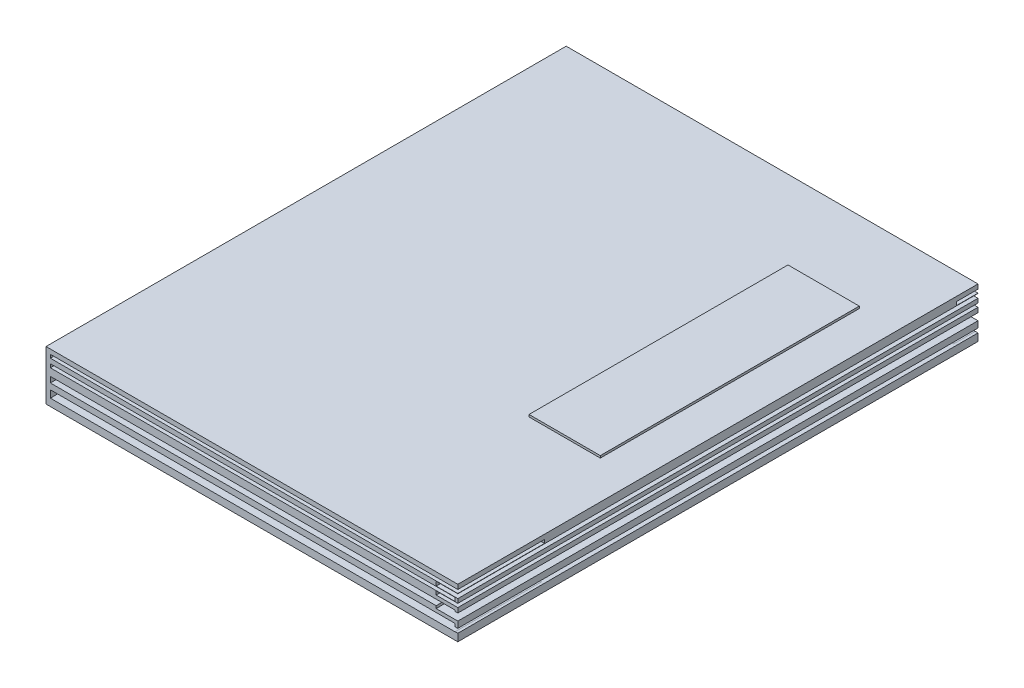
SolidWorks part; units mm, degrees
ref_plane "前视基准面" through (0, 0, 0) normal (0, 0, 1) x (1, 0, 0)
ref_plane "上视基准面" through (0, 0, 0) normal (0, 1, 0) x (1, 0, 0)
ref_plane "右视基准面" through (0, 0, 0) normal (1, 0, 0) x (0, 0, -1)
sketch "草图1" plane through (0, 0, 0) normal (0, 1, 0) x (1, 0, 0)
  line L1 (-95, 125) -> (95, 125)
  line L2 (-95, 125) -> (-95, -115)
  line L3 (-95, -115) -> (95, -115)
  line L4 (95, 125) -> (95, -115)
  point P0 (0, 0)
extrude "凸台-拉伸1" add sketch "草图1" along normal blind 23
sketch "草图2" plane through (95, 0, 0) normal (1, 0, 0) x (0, 0, -1)
  line L1 (128.5392, 19.1887) -> (-116.4147, 19.1887)
  line L2 (128.5392, 19.1887) -> (128.5392, 17.2678)
  line L3 (128.5392, 17.2678) -> (-116.4147, 17.2678)
  line L4 (-116.4147, 19.1887) -> (-116.4147, 17.2678)
  line L5 (129.0094, 15.3627) -> (-116.7119, 15.3627)
  line L6 (129.0094, 15.3627) -> (129.0094, 13.679)
  line L7 (129.0094, 13.679) -> (-116.7119, 13.679)
  line L8 (-116.7119, 15.3627) -> (-116.7119, 13.679)
  line L9 (127.8189, 8.2957) -> (-116.7119, 8.2957)
  line L10 (127.8189, 8.2957) -> (127.8189, 11.5)
  line L11 (127.8189, 11.5) -> (-116.7119, 11.5)
  line L12 (-116.7119, 8.2957) -> (-116.7119, 11.5)
  line L13 (127.0838, 5.3696) -> (-116.4565, 5.3696)
  line L14 (127.0838, 5.3696) -> (127.0838, 3.4251)
  line L15 (127.0838, 3.4251) -> (-116.4565, 3.4251)
  line L16 (-116.4565, 5.3696) -> (-116.4565, 3.4251)
extrude "切除-拉伸1" cut sketch "草图2" against normal blind 10
sketch "草图3" plane through (0, 0, 115) normal (0, 0, 1) x (1, 0, 0)
  line L0 (95, 23) -> (95, 19.1887) construction
  line L1 (95, 19.3299) -> (-92.994, 19.3299)
  line L2 (95, 19.3299) -> (95, 20.9016)
  line L3 (95, 20.9016) -> (-92.994, 20.9016)
  line L4 (-92.994, 19.3299) -> (-92.994, 20.9016)
  line L6 (93.7585, 17.1483) -> (-92.994, 17.1483)
  line L7 (93.7585, 17.1483) -> (93.7585, 15.4844)
  line L8 (93.7585, 15.4844) -> (-92.994, 15.4844)
  line L9 (-92.994, 17.1483) -> (-92.994, 15.4844)
  line L10 (93.7585, 12.0577) -> (-92.994, 12.0577)
  line L11 (93.7585, 12.0577) -> (93.7585, 9.4388)
  line L12 (93.7585, 9.4388) -> (-92.994, 9.4388)
  line L13 (-92.994, 12.0577) -> (-92.994, 9.4388)
  line L14 (93.7585, 6.7145) -> (-92.994, 6.7145)
  line L15 (93.7585, 6.7145) -> (93.7585, 3.3684)
  line L16 (93.7585, 3.3684) -> (-92.994, 3.3684)
  line L17 (-92.994, 6.7145) -> (-92.994, 3.3684)
extrude "切除-拉伸2" cut sketch "草图3" against normal blind 40
sketch "草图4" plane through (0, 23, 0) normal (0, 1, 0) x (1, 0, 0)
  line L0 (-156.583, 0) -> (142.6497, 0) construction
ref_plane "基准面1" through (0, 0, 0) normal (0, 0, 1) x (1, 0, 0)
ref_plane "基准面2" through (0, 0, -20) normal (0, 0, 1) x (1, 0, 0)
mirror "镜向3" about plane through (0, 0, -20) normal (0, 0, 1) of "切除-拉伸2"
ref_plane "基准面3" through (0, 23, 0) normal (0, 1, 0) x (1, 0, 0)
sketch "草图7" plane through (0, 23, 0) normal (0, 1, 0) x (1, 0, 0)
  line L0 (-80.2819, 125) -> (-80.2819, -115)
  line L1 (95, 125) -> (-95, 125) construction
  line L2 (-95, -115) -> (95, -115) construction
  line L3 (-80.2819, -115) -> (-77.7275, -115)
  line L4 (-77.7275, -115) -> (-77.7275, 125)
  line L5 (-77.7275, 125) -> (-80.2819, 125)
  line L6 (-95, 102.2628) -> (-80.2819, 102.2628)
  line L7 (-95, 125) -> (-95, -115) construction
  line L8 (-95, 62.5024) -> (-80.2819, 62.5024)
  line L9 (-95, 20.5533) -> (-80.2819, 20.5533)
  line L10 (-95, -11.1821) -> (-80.2819, -11.1821)
  line L11 (-95, -49.8483) -> (-80.2819, -49.8483)
  line L12 (-95, -85.5962) -> (-80.2819, -85.5962)
ref_plane "基准面4" through (-95, 0, 0) normal (-1, 0, 0) x (0, 0, 1)
sketch "草图8" plane through (-95, 0, 0) normal (-1, 0, 0) x (0, 0, 1)
  line L0 (-102.2628, 23) -> (-102.2628, 0)
  line L1 (-125, 0) -> (115, 0) construction
  line L2 (-62.5024, 23) -> (-62.5024, 0)
  line L3 (-20.5533, 23) -> (-20.5533, 0)
  line L4 (11.1821, 23) -> (11.1821, 0)
  line L5 (49.8483, 23) -> (49.8483, 0)
  line L6 (85.5962, 23) -> (85.5962, 0)
sketch "草图9" plane through (0, 0, 0) normal (0, -1, 0) x (1, 0, 0)
  line L0 (-77.7275, 115) -> (-77.7275, -125)
  line L1 (-95, 85.5962) -> (-77.7275, 85.5962)
  line L2 (-95, 49.8483) -> (-77.7275, 49.8483)
  line L3 (-95, 11.1821) -> (-77.7275, 11.1821)
  line L4 (-95, -20.5533) -> (-77.7275, -20.5533)
  line L5 (-95, -62.5024) -> (-77.7275, -62.5024)
  line L6 (-94.9153, -101.4933) -> (-77.7275, -101.4933)
sketch "草图10" plane through (0, 23, 0) normal (0, 1, 0) x (1, 0, 0)
  line L1 (44.5752, 87.7564) -> (77.4585, 87.7564)
  line L2 (44.5752, 87.7564) -> (44.5752, -31.7197)
  line L3 (44.5752, -31.7197) -> (77.4585, -31.7197)
  line L4 (77.4585, 87.7564) -> (77.4585, -31.7197)
extrude "凸台-拉伸2" add sketch "草图10" along normal blind 1
